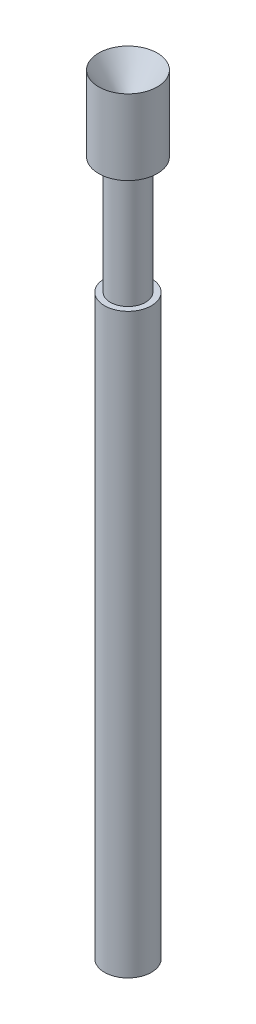
SolidWorks part; units mm, degrees
ref_plane "Front Plane" through (0, 0, 0) normal (0, 0, 1) x (1, 0, 0)
ref_plane "Top Plane" through (0, 0, 0) normal (0, 1, 0) x (1, 0, 0)
ref_plane "Right Plane" through (0, 0, 0) normal (1, 0, 0) x (0, 0, -1)
sketch "Sketch1" plane through (0, 0, 0) normal (0, 0, 1) x (1, 0, 0)
  line L0 (0, 0) -> (0.508, 0)
  line L1 (0.508, 0) -> (0.508, 12.4968)
  line L2 (0.508, 12.4968) -> (0.381, 12.4968)
  line L3 (0.381, 12.4968) -> (0.381, 15.0368)
  line L4 (0.381, 15.0368) -> (0.635, 15.0368)
  line L5 (0.635, 15.0368) -> (0.635, 16.6624)
  line L7 (0, 15.9004) -> (0, 0)
  line L8 (0, 18.2856) -> (0, -0.9214) construction
  line L9 (0.635, 16.6624) -> (0.127, 15.9004)
  line L10 (0.127, 15.9004) -> (0, 15.9004)
  dimension "D1" = 1.016
  dimension "D2" = 0.762
  dimension "D3" = 1.27
  dimension "D4" = 12.4968
  dimension "D5" = 1.6256
  dimension "D6" = 2.54
  dimension "D7" = 0.254
  dimension "D8" = 0.762
revolve "Revolve1" add sketch "Sketch1" angle 360 about L8
